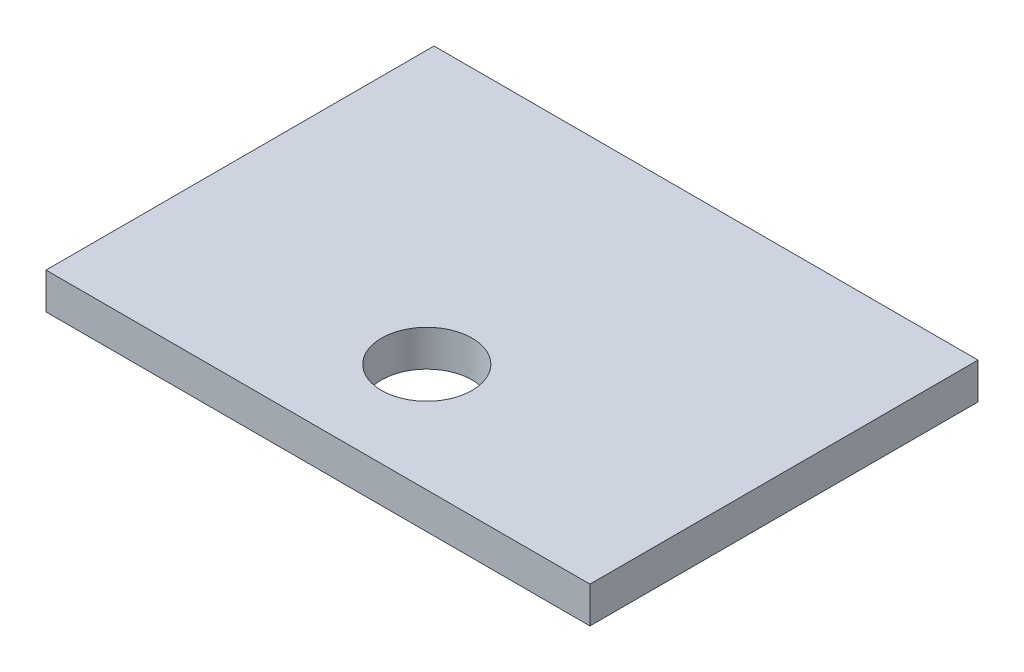
SolidWorks part; units mm, degrees
ref_plane "前视基准面" through (0, 0, 0) normal (0, 0, 1) x (1, 0, 0)
ref_plane "上视基准面" through (0, 0, 0) normal (0, 1, 0) x (1, 0, 0)
ref_plane "右视基准面" through (0, 0, 0) normal (1, 0, 0) x (0, 0, -1)
sketch "草图1" plane through (0, 0, 0) normal (0, 1, 0) x (1, 0, 0)
  line L1 (-7.5, 5.35) -> (7.5, 5.35)
  line L2 (-7.5, 5.35) -> (-7.5, -5.35)
  line L3 (-7.5, -5.35) -> (7.5, -5.35)
  line L4 (7.5, 5.35) -> (7.5, -5.35)
  line L5 (-7.5, 5.35) -> (7.5, -5.35) construction
  line L6 (-7.5, -5.35) -> (7.5, 5.35) construction
  circle A1 centre (0, -2.35) radius 1.25
  point P0 (0, 0)
  dimension "D5" = 2.5
  dimension "D1" = 15
  dimension "D2" = 10.7
  dimension "D3" = 7.5
  dimension "D4" = 3
extrude "凸台-拉伸1" add sketch "草图1" along normal blind 1
